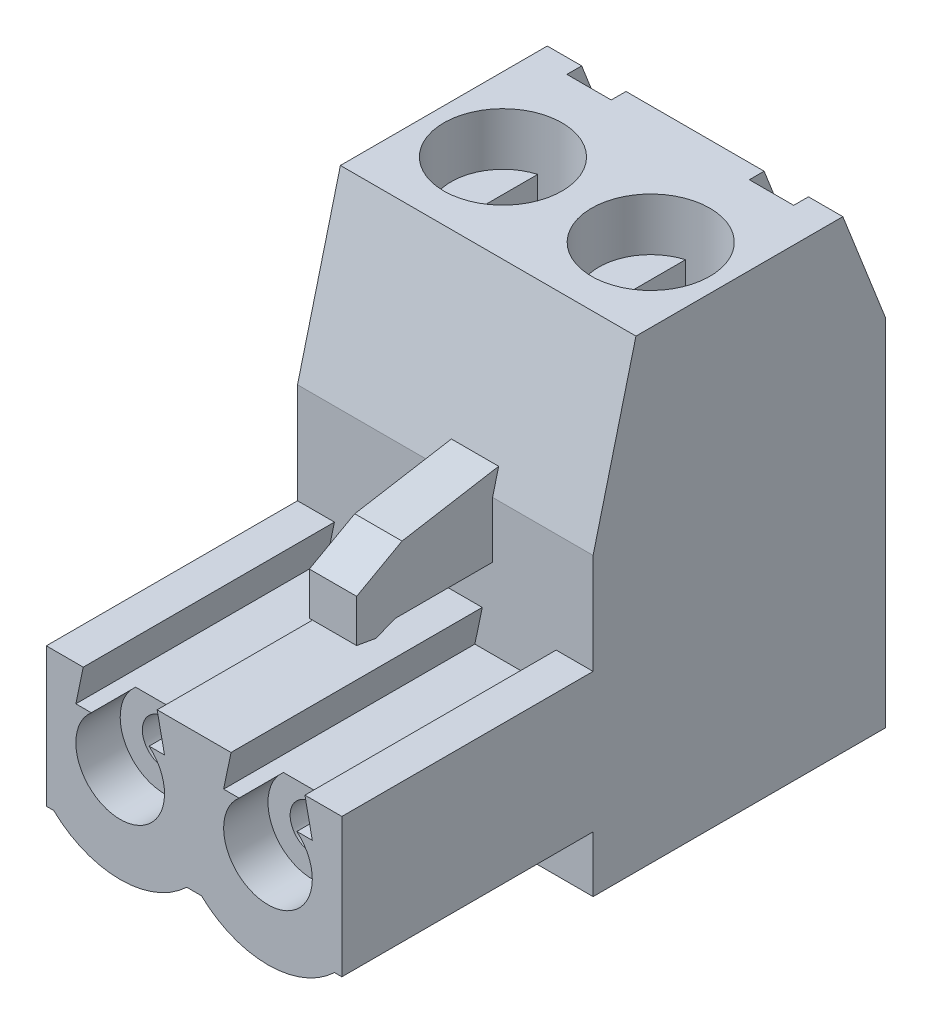
SolidWorks part; units mm, degrees
ref_plane "Ebene vorne" through (0, 0, 0) normal (0, 0, 1) x (1, 0, 0)
ref_plane "Ebene oben" through (0, 0, 0) normal (0, 1, 0) x (1, 0, 0)
ref_plane "Ebene rechts" through (0, 0, 0) normal (1, 0, 0) x (0, 0, -1)
sketch "Skizze1" plane through (0, 0, 0) normal (1, 0, 0) x (0, 0, -1)
  line L0 (0, 0) -> (0, 15.7) construction
  line L1 (3.5, 15.7) -> (-3.5, 15.7)
  line L2 (-3.5, 15.7) -> (-4.95, 10)
  line L3 (-4.95, 10) -> (-4.95, 0)
  line L4 (-4.95, 0) -> (4.95, 0)
  line L5 (4.95, 12) -> (4.95, 0)
  line L6 (3.5, 15.7) -> (4.95, 12)
  dimension "D1" = 15.7
  dimension "D2" = 9.9
  dimension "D3" = 7
  dimension "D4" = 10
  dimension "D5" = 12
extrude "Aufsatz-Linear austragen1" add sketch "Skizze1" along normal blind 10
sketch "Skizze2" plane through (0, 0, 4.95) normal (0, 0, 1) x (1, 0, 0)
  line L0 (5, 10) -> (5, 0) construction
  line L1 (10, 10) -> (0, 10) construction
  line L2 (10, 0) -> (0, 0) construction
  line L3 (4.75, 1.9) -> (5.25, 1.9)
  line L4 (2.5, 0) -> (2.5, 4.2625) construction
  line L5 (0.25, 1.9) -> (0, 1.9)
  line L6 (0, 10) -> (0, 0) construction
  line L8 (9.75, 1.9) -> (9.75, 3.3198) construction
  line L9 (7.5, 0) -> (7.5, 4.2625) construction
  line L10 (9.75, 1.9) -> (10, 1.9)
  line L11 (0, 1) -> (10, 1) construction
  line L12 (10, 10) -> (10, 0) construction
  line L13 (0, 1.9) -> (0, 6.6)
  line L14 (0, 6.6) -> (10, 6.6)
  line L15 (10, 6.6) -> (10, 1.9)
  arc A0 (4.75, 1.9) -> (0.25, 1.9) centre (2.5, 4.2625) cw
  arc A1 (5.25, 1.9) -> (9.75, 1.9) centre (7.5, 4.2625) ccw
  point P17 (2.5, 3.2669)
  point P21 (5, 1.9)
  dimension "D1" = 0.5
  dimension "D2" = 1
  dimension "D3" = 5.6
  dimension "D4" = 4.7
extrude "Aufsatz-Linear austragen2" add sketch "Skizze2" along normal blind 18.4 from surface at -9.9 starting at face at (5, 6, -4.95)
sketch "Skizze3" plane through (0, 0, 13.45) normal (0, 0, 1) x (1, 0, 0)
  line L0 (1.25, 6.6) -> (1, 5.4)
  line L1 (10, 6.6) -> (0, 6.6) construction
  line L2 (1, 5.4) -> (4, 5.4)
  line L3 (2.5, 5.4) -> (2.5, 6.6) construction
  line L4 (1.25, 6.6) -> (3.75, 6.6)
  line L5 (3.75, 6.6) -> (4, 5.4)
  line L6 (5, 1.9) -> (5, 6.6) construction
  line L7 (4.75, 1.9) -> (5.25, 1.9) construction
  line L8 (7.5, 5.4) -> (7.5, 6.6) construction
  line L9 (6.25, 6.6) -> (6, 5.4)
  line L10 (8.75, 6.6) -> (6.25, 6.6)
  line L11 (9, 5.4) -> (6, 5.4)
  line L12 (8.75, 6.6) -> (9, 5.4)
  line L13 (2.5, 1) -> (2.5, 5.4) construction
  arc A1 (0.25, 1.9) -> (4.75, 1.9) centre (2.5, 4.2625) ccw construction
  point P19 (2.5, 1)
  point P23 (4, 5.4635)
  dimension "D1" = 2.5
  dimension "D2" = 2
  dimension "D3" = 1.2
extrude "Schnitt-Linear austragen1" cut sketch "Skizze3" against normal up to surface (8.5 mm away) up to face at (5, 8.3, 4.95)
sketch "Skizze4" plane through (0, 0, 13.45) normal (0, 0, 1) x (1, 0, 0)
  line L0 (2.5, 1) -> (2.5, 4.2625) construction
  line L1 (5, 6.6) -> (5, 0) construction
  line L2 (6.25, 6.6) -> (3.75, 6.6) construction
  line L3 (10, 0) -> (0, 0) construction
  line L4 (1, 4.2625) -> (1, 0.6357) construction
  line L5 (9, 4.2625) -> (9, 0.6357) construction
  line L6 (7.5, 1) -> (7.5, 4.2625) construction
  circle A0 centre (2.5, 4.2625) radius 1.5
  arc A1 (0.25, 1.9) -> (4.75, 1.9) centre (2.5, 4.2625) ccw construction
  arc A2 (0.25, 1.9) -> (4.75, 1.9) centre (2.5, 4.2625) ccw construction
  circle A3 centre (7.5, 4.2625) radius 1.5
  point P22 (8.8825, 4.8309)
  dimension "D1" = 8
extrude "Schnitt-Linear austragen2" cut sketch "Skizze4" against normal blind 1.5
sketch "Skizze5" plane through (10, 0, 0) normal (1, 0, 0) x (0, 0, -1)
  line L0 (-4.7445, 10.8077) -> (-8.0141, 10.2511)
  line L1 (-3.5, 15.7) -> (-4.95, 10) construction
  line L2 (-8.0141, 10.2511) -> (-9.55, 9.4)
  line L3 (-9.55, 9.4) -> (-9.55, 7.9567)
  line L4 (-9.55, 7.9567) -> (-8.8987, 7.8424)
  line L5 (-8.8987, 7.8424) -> (-8.2474, 8.1)
  line L6 (-8.2474, 8.1) -> (-4.95, 8.1)
  line L7 (-4.95, 10) -> (-4.95, 6.6) construction
  line L8 (-4.95, 8.1) -> (-4.95, 10)
  line L9 (-4.95, 10) -> (-4.7445, 10.8077)
  line L10 (-13.45, 6.6) -> (-4.95, 6.6) construction
  line L11 (-9.55, 9.0477) -> (-8.2474, 9.0477) construction
  line L12 (-8.2474, 9.0477) -> (-8.2474, 8.1) construction
  line L13 (-8.8987, 9.0477) -> (-8.8987, 7.8424) construction
  point P17 (-9.55, 7.9567)
  point P19 (-4.7445, 10.8077)
  point P20 (-8.0141, 10.2511)
  dimension "D1" = 4.6
  dimension "D2" = 2.8
  dimension "D3" = 1.5
extrude "Aufsatz-Linear austragen4" add sketch "Skizze5" against normal through all
sketch "Skizze6" plane through (0, 0, 4.95) normal (0, 0, 1) x (1, 0, 0)
  line L0 (0, 15.7) -> (0, 10.8077) construction
  line L1 (0, 15.7) -> (5, 15.7)
  line L2 (0, 15.7) -> (0, 7.2479)
  line L3 (0, 7.2479) -> (5, 7.2479)
  line L4 (5, 15.7) -> (5, 7.2479)
  line L5 (10, 15.7) -> (0, 15.7) construction
  line L7 (10, 15.7) -> (6.6, 15.7)
  line L8 (10, 15.7) -> (10, 7.2479)
  line L9 (10, 7.2479) -> (6.6, 7.2479)
  line L10 (6.6, 15.7) -> (6.6, 7.2479)
  dimension "D1" = 1.6
extrude "Schnitt-Linear austragen3" cut sketch "Skizze6" against normal up to surface and the other way through all up to face at (5, 13.2539, 4.1223)
sketch "Skizze7" plane through (0, 15.7, 0) normal (0, 1, 0) x (1, 0, 0)
  line L0 (10, 3.5) -> (0, 3.5) construction
  line L1 (2.6636, 3) -> (1.1636, 3)
  line L2 (2.6636, 3) -> (2.6636, 4)
  line L3 (2.6636, 4) -> (1.1636, 4)
  line L4 (1.1636, 3) -> (1.1636, 4)
  line L5 (2.6636, 3) -> (1.1636, 4) construction
  line L6 (2.6636, 4) -> (1.1636, 3) construction
  line L7 (5, 4.95) -> (5, -3.5) construction
  line L8 (10, 4.95) -> (0, 4.95) construction
  line L9 (10, -3.5) -> (0, -3.5) construction
  line L10 (7.3364, 4) -> (8.8364, 3) construction
  line L11 (7.3364, 3) -> (8.8364, 4) construction
  line L12 (8.8364, 3) -> (8.8364, 4)
  line L13 (7.3364, 4) -> (8.8364, 4)
  line L14 (7.3364, 3) -> (7.3364, 4)
  line L15 (7.3364, 3) -> (8.8364, 3)
  point P0 (1.9136, 3.5)
  point P17 (8.0864, 3.5)
  dimension "D1" = 1.5
  dimension "D2" = 1
extrude "Schnitt-Linear austragen4" cut sketch "Skizze7" against normal blind 1.5
sketch "Skizze8" plane through (0, 15.7, 0) normal (0, 1, 0) x (1, 0, 0)
  line L0 (0, -0.5) -> (5, -0.5) construction
  line L2 (0, 3.5) -> (0, -3.5) construction
  line L3 (10, -3.5) -> (0, -3.5) construction
  line L4 (5, -3.5) -> (5, 3.5) construction
  line L5 (7.3364, 3.5) -> (2.6636, 3.5) construction
  circle A0 centre (2.5, -0.5) radius 2
  circle A1 centre (7.5, -0.5) radius 2
  point P3 (5, 0)
  point P4 (0, 0)
  point P13 (0.5865, 0)
  point P14 (0, -1.1066)
  point P17 (5, -1.1836)
  dimension "D1" = 4
  dimension "D2" = 0.5
extrude "Schnitt-Linear austragen5" cut sketch "Skizze8" against normal blind 4
sketch "Skizze9" plane through (0, 0, -4.95) normal (0, 0, -1) x (-1, 0, 0)
  line L0 (-10, 9.7001) -> (-5, 9.7001) construction
  line L1 (-10, 0) -> (-10, 12) construction
  line L2 (-5, 9.7001) -> (-5, 15.7) construction
  line L3 (-7.3364, 15.7) -> (-2.6636, 15.7) construction
  line L4 (-7.5, 9.7001) -> (-7.5, 0) construction
  line L5 (-10, 0) -> (0, 0) construction
  line L6 (-4, 5.8217) -> (-1, 1.8217) construction
  line L7 (-6, 1.8217) -> (-9, 1.8217)
  line L8 (-6, 1.8217) -> (-6, 5.8217)
  line L9 (-6, 5.8217) -> (-9, 5.8217)
  line L10 (-9, 1.8217) -> (-9, 5.8217)
  line L11 (-6, 1.8217) -> (-9, 5.8217) construction
  line L12 (-6, 5.8217) -> (-9, 1.8217) construction
  line L13 (-4, 1.8217) -> (-1, 5.8217) construction
  line L14 (-1, 1.8217) -> (-1, 5.8217)
  line L15 (-4, 5.8217) -> (-1, 5.8217)
  line L16 (-4, 1.8217) -> (-4, 5.8217)
  line L17 (-4, 1.8217) -> (-1, 1.8217)
  point P11 (-7.5, 3.8217)
  point P20 (-2.5, 3.8217)
  dimension "D1" = 2
  dimension "D2" = 4
extrude "Schnitt-Linear austragen6" cut sketch "Skizze9" against normal blind 5
sketch "Skizze10" plane through (0, 0, 11.95) normal (0, 0, 1) x (1, 0, 0)
  line L1 (5, 6.6) -> (5, 1.9) construction
  line L2 (6.25, 6.6) -> (3.75, 6.6) construction
  line L3 (4.75, 1.9) -> (5.25, 1.9) construction
  circle A0 centre (2.5, 4.2625) radius 0.75
  circle A2 centre (7.5, 4.2625) radius 0.75
  dimension "D1" = 1.5
extrude "Schnitt-Linear austragen7" cut sketch "Skizze10" against normal up to surface (7 mm away) up to face at (5.2, 7.3375, 4.95)
chamfer "Fase1" distance 2 angle 45 2 edges at (7.5, 5.8217, -4.95) (2.5, 5.8217, -4.95)
sketch "Skizze11" plane through (0, 1.8217, 0) normal (0, 1, 0) x (1, 0, 0)
  line L0 (6, -0.05) -> (6, 4.95) construction
  line L1 (6, 2.45) -> (9, 2.45)
  line L2 (6, 2.45) -> (6, 0)
  line L3 (6, 0) -> (9, 0)
  line L4 (9, 2.45) -> (9, 0)
  line L5 (9, -0.05) -> (9, 4.95) construction
  line L6 (4, -0.05) -> (4, 4.95) construction
  line L7 (4, 2.45) -> (1, 2.45)
  line L8 (4, 2.45) -> (4, -0.05)
  line L9 (4, -0.05) -> (1, -0.05)
  line L10 (1, 2.45) -> (1, -0.05)
  line L11 (1, -0.05) -> (1, 4.95) construction
  line L12 (4, 2.45) -> (6, 2.45) construction
  line L13 (4, 4.95) -> (1, 4.95) construction
  dimension "D1" = 2.5
extrude "Aufsatz-Linear austragen5" add sketch "Skizze11" along normal offset from surface (3 mm away) 1 up to face at (2.5, 5.8217, -1.45)
sketch "Skizze12" plane through (0, 11.7, 0) normal (0, 1, 0) x (1, 0, 0)
  line L0 (5, 3.5) -> (5, -3.5) construction
  line L1 (7.3364, 3.5) -> (2.6636, 3.5) construction
  line L2 (10, -3.5) -> (0, -3.5) construction
  circle A0 centre (7.5, -0.5) radius 1.75
  circle A1 centre (2.5, -0.5) radius 1.75
  circle A2 centre (2.5, -0.5) radius 2 construction
  dimension "D1" = 0.25
extrude "Aufsatz-Linear austragen6" add sketch "Skizze12" along normal offset from surface (1.4 mm away) 2.6 up to face at (2.5, 15.7, 2.5)
sketch "Skizze13" plane through (0, 13.1, 0) normal (0, 1, 0) x (1, 0, 0)
  line L1 (2, 1.1771) -> (2, -2.1771)
  line L2 (5, 4.95) -> (5, -2.1489) construction
  line L3 (10, 4.95) -> (0, 4.95) construction
  line L5 (2.5, 1.25) -> (2.5, -0.5) construction
  line L7 (3, 1.1771) -> (3, -2.1771)
  line L8 (7, 1.1771) -> (7, -2.1771)
  line L9 (8, 1.1771) -> (8, -2.1771)
  arc A5 (2, 1.1771) -> (2, -2.1771) centre (2.5, -0.5) ccw
  circle A6 centre (2.5, -0.5) radius 1.75 construction
  circle A7 centre (2.5, -0.5) radius 1.75 construction
  arc A8 (3, 1.1771) -> (3, -2.1771) centre (2.5, -0.5) cw
  arc A9 (7, 1.1771) -> (7, -2.1771) centre (7.5, -0.5) ccw
  arc A10 (8, 1.1771) -> (8, -2.1771) centre (7.5, -0.5) cw
  dimension "D1" = 1
extrude "Aufsatz-Linear austragen7" add sketch "Skizze13" along normal offset from surface (1 mm away) 1.6 separate body up to face at (2.5, 15.7, 2.5)
